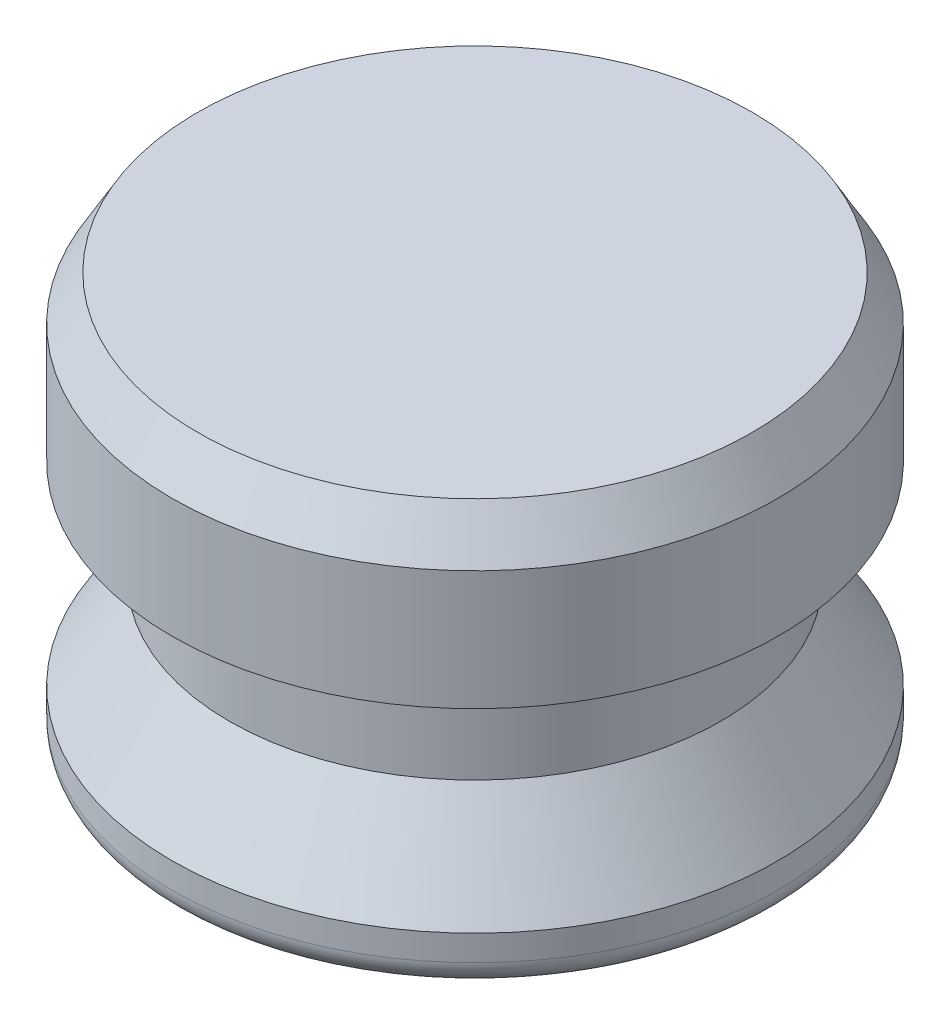
SolidWorks part; units mm, degrees
ref_plane "Front Plane" through (0, 0, 0) normal (0, 0, 1) x (1, 0, 0)
ref_plane "Top Plane" through (0, 0, 0) normal (0, 1, 0) x (1, 0, 0)
ref_plane "Right Plane" through (0, 0, 0) normal (1, 0, 0) x (0, 0, -1)
sketch "Sketch1" plane through (0, 0, 0) normal (0, 0, 1) x (1, 0, 0)
  line L0 (0, 0) -> (0, 12.7) construction
  line L1 (0, 0) -> (-9.398, 0)
  line L2 (-9.398, 0) -> (-9.398, 1.5875)
  line L4 (-7.62, 4.445) -> (-7.62, 7.62)
  line L5 (-7.62, 7.62) -> (-9.398, 7.62)
  line L6 (-9.398, 7.62) -> (-9.398, 12.7)
  line L7 (-9.398, 12.7) -> (0, 12.7)
  line L8 (-9.525, 16.6801) -> (-9.525, -9.6051) construction
  line L9 (0, 0) -> (0, 12.7)
  line L10 (-7.62, 4.445) -> (-9.398, 1.5875)
  dimension "D1" = 12.7
  dimension "D2" = 9.398
  dimension "D3" = 3.175
  dimension "D4" = 1.5875
  dimension "D5" = 9.525
  dimension "D6" = 7.62
  dimension "D7" = 7.62
revolve "Revolve1" add sketch "Sketch1" angle 360 about L9
fillet "Fillet1" radius 0.7937 1 edges at (0, 0, -9.398)
chamfer "Chamfer1" distance 0.7937 angle 60 1 edges at (0, 12.7, -9.398)
